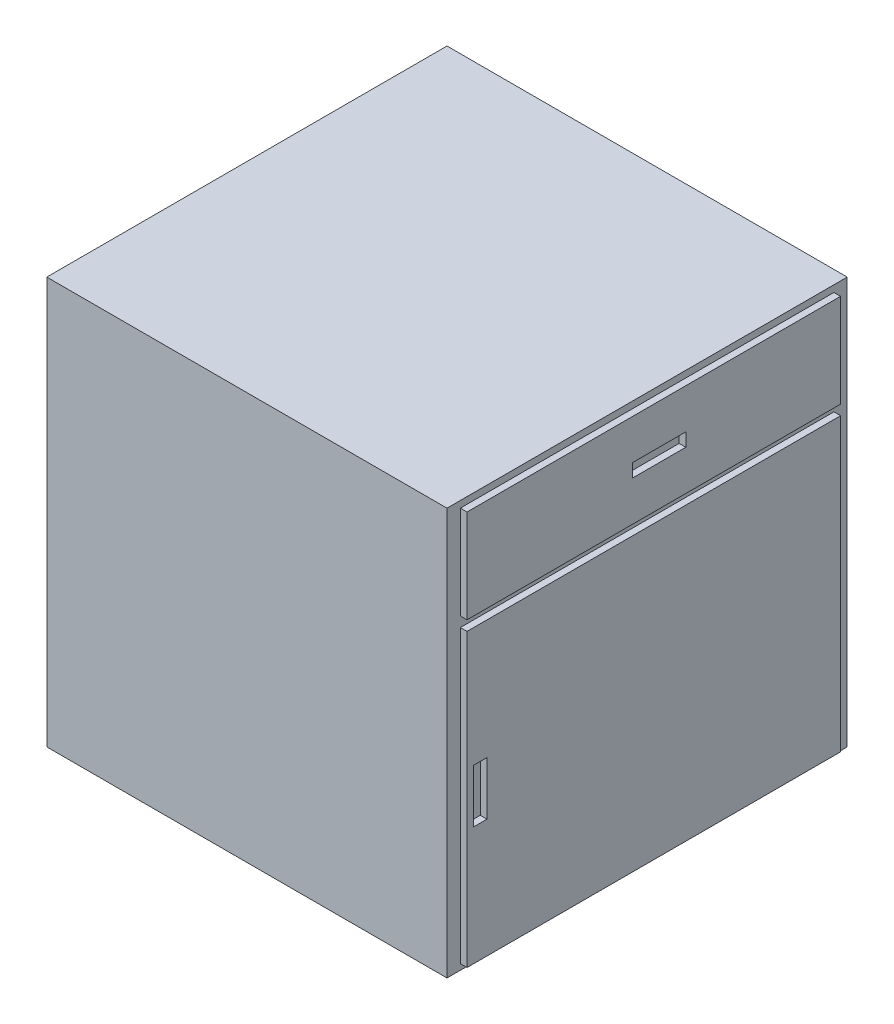
SolidWorks part; units mm, degrees
ref_plane "Front Plane" through (0, 0, 0) normal (0, 0, 1) x (1, 0, 0)
ref_plane "Top Plane" through (0, 0, 0) normal (0, 1, 0) x (1, 0, 0)
ref_plane "Right Plane" through (0, 0, 0) normal (1, 0, 0) x (0, 0, -1)
sketch "Sketch1" plane through (0, 0, 0) normal (0, 0, 1) x (1, 0, 0)
  line L1 (0, 0) -> (-600, 0)
  line L2 (0, 0) -> (0, -610)
  line L3 (0, -610) -> (-600, -610)
  line L4 (-600, 0) -> (-600, -610)
  dimension "D1" = 610
  dimension "D2" = 600
extrude "Boss-Extrude1" add sketch "Sketch1" along normal blind 600
sketch "Sketch2" plane through (0, 0, 0) normal (1, 0, 0) x (0, 0, -1)
  line L0 (0, -610) -> (0, 0) construction
  line L1 (-580, -9.9966) -> (-20, -9.9966)
  line L2 (-580, -9.9966) -> (-580, -149.9966)
  line L3 (-580, -149.9966) -> (-20, -149.9966)
  line L4 (-20, -9.9966) -> (-20, -149.9966)
  line L5 (-580, -164.9966) -> (-20, -164.9966)
  line L6 (-580, -164.9966) -> (-580, -601.4365)
  line L7 (-580, -601.4365) -> (-20, -601.4365)
  line L8 (-20, -164.9966) -> (-20, -601.4365)
  line L9 (-570, -343.759) -> (-550, -343.759)
  line L10 (-570, -343.759) -> (-570, -423.759)
  line L11 (-570, -423.759) -> (-550, -423.759)
  line L12 (-550, -343.759) -> (-550, -423.759)
  line L13 (-332, -69.9605) -> (-252, -69.9605)
  line L14 (-332, -69.9605) -> (-332, -89.9605)
  line L15 (-332, -89.9605) -> (-252, -89.9605)
  line L16 (-252, -69.9605) -> (-252, -89.9605)
  line L17 (-600, -610) -> (-600, 0) construction
  dimension "D1" = 140
  dimension "D2" = 15
  dimension "D3" = 20
  dimension "D4" = 80
  dimension "D5" = 248
  dimension "D6" = 20
  dimension "D7" = 20
  dimension "D8" = 20
  dimension "D9" = 80
  dimension "D10" = 10
extrude "Boss-Extrude2" add sketch "Sketch2" along normal blind 10
